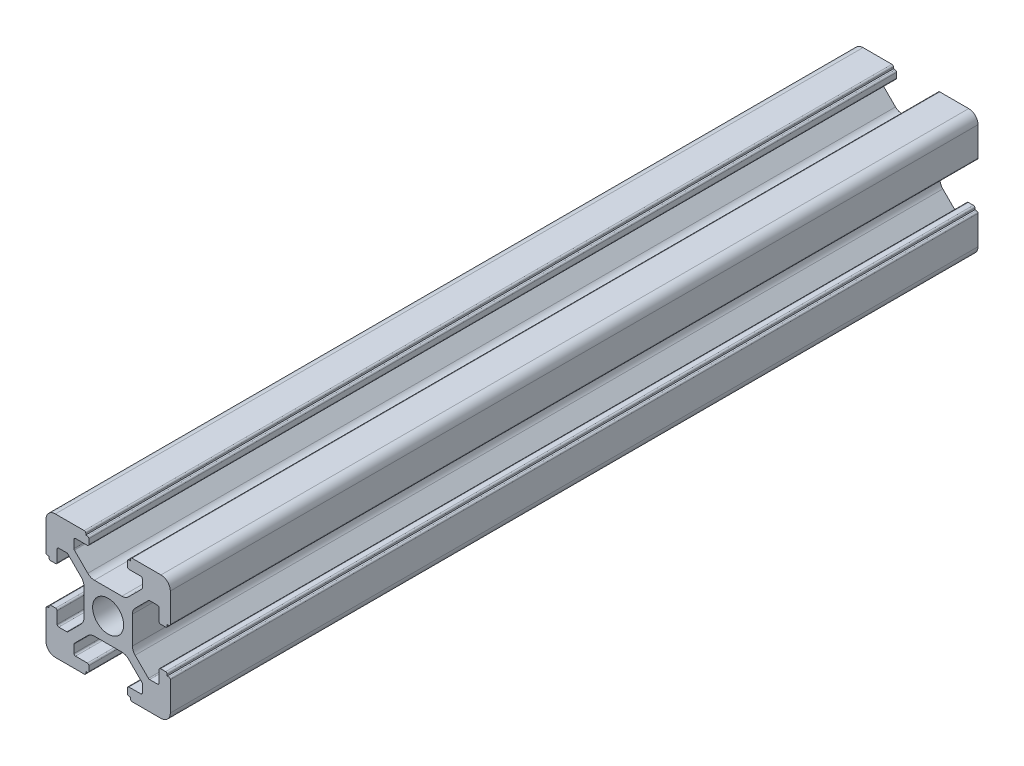
SolidWorks part; units mm, degrees
material "1060 Alloy"
ref_plane "前视基准面" through (0, 0, 0) normal (0, 0, 1) x (1, 0, 0)
ref_plane "上视基准面" through (0, 0, 0) normal (0, 1, 0) x (1, 0, 0)
ref_plane "右视基准面" through (0, 0, 0) normal (1, 0, 0) x (0, 0, -1)
sketch "草图1" plane through (0, 0, 0) normal (0, 0, 1) x (1, 0, 0)
  line L0 (0, 0) -> (0, 5.5) construction
  line L1 (-8.5023, -10.0023) -> (-3.85, -10.0023)
  line L2 (-10.0023, -8.5023) -> (-10.0023, -3.85)
  line L3 (-8.5023, 10.0023) -> (-3.85, 10.0023)
  line L4 (10.0023, -8.5023) -> (10.0023, -3.85)
  line L5 (-10.0023, -10.0023) -> (10.0023, 10.0023) construction
  line L6 (-10.0023, 10.0023) -> (10.0023, -10.0023) construction
  line L7 (-2.218, -3.9) -> (2.218, -3.9)
  line L8 (-3.9, -2.218) -> (-3.9, 2.218)
  line L9 (-2.218, 3.9) -> (2.218, 3.9)
  line L10 (3.9, -2.218) -> (3.9, 2.218)
  line L11 (-3.9, -3.9) -> (3.9, 3.9) construction
  line L12 (-3.9, 3.9) -> (3.9, -3.9) construction
  line L13 (-5.25, -8.2) -> (-3.35, -8.2)
  line L14 (-8.2, -5.25) -> (-8.2, -3.35)
  line L15 (-5.25, 8.2) -> (-3.35, 8.2)
  line L16 (8.2, -5.25) -> (8.2, -3.35)
  line L17 (-8.2, -8.2) -> (8.2, 8.2) construction
  line L18 (-8.2, 8.2) -> (8.2, -8.2) construction
  line L19 (-7.95, 5.5) -> (-6.6642, 5.5)
  line L20 (0, 0) -> (5.5, 0) construction
  line L23 (-5.5, 7.95) -> (-5.5, 6.6642)
  line L26 (0, 0) -> (-0.5303, 0.5303)
  line L27 (3.2787, 4.3393) -> (5.4268, 6.4874)
  line L28 (0, 0) -> (0.5303, -0.5303)
  line L29 (5.5, 6.6642) -> (5.5, 7.95)
  line L30 (4.3393, 3.2787) -> (6.4874, 5.4268)
  line L31 (6.6642, 5.5) -> (7.95, 5.5)
  line L32 (4.3393, -3.2787) -> (6.4874, -5.4268)
  line L33 (3.2787, -4.3393) -> (5.4268, -6.4874)
  line L34 (-3.2787, -4.3393) -> (-5.4268, -6.4874)
  line L35 (-4.3393, -3.2787) -> (-6.4874, -5.4268)
  line L36 (-4.3393, 3.2787) -> (-6.4874, 5.4268)
  line L37 (-3.2787, 4.3393) -> (-5.4268, 6.4874)
  line L38 (3.1, -8.45) -> (3.1, -9.2523)
  line L39 (8.45, 3.1) -> (9.2523, 3.1)
  line L40 (-5.5, -6.6642) -> (-5.5, -7.95)
  line L41 (-6.6642, -5.5) -> (-7.95, -5.5)
  line L42 (5.5, -6.6642) -> (5.5, -7.95)
  line L43 (6.6642, -5.5) -> (7.95, -5.5)
  line L44 (9.2523, -3.1) -> (8.45, -3.1)
  line L46 (10.0023, 3.85) -> (10.0023, 8.5023)
  line L47 (8.2, 3.35) -> (8.2, 5.25)
  line L48 (-3.1, -9.2523) -> (-3.1, -8.45)
  line L49 (-8.45, -3.1) -> (-9.2523, -3.1)
  line L50 (-9.2523, 3.1) -> (-8.45, 3.1)
  line L51 (-3.1, 8.45) -> (-3.1, 9.2523)
  line L52 (3.1, 9.2523) -> (3.1, 8.45)
  line L53 (3.85, 10.0023) -> (8.5023, 10.0023)
  line L54 (3.35, 8.2) -> (5.25, 8.2)
  line L55 (-10.0023, 3.85) -> (-10.0023, 8.5023)
  line L56 (-8.2, 3.35) -> (-8.2, 5.25)
  line L57 (3.35, -8.2) -> (5.25, -8.2)
  line L58 (3.85, -10.0023) -> (8.5023, -10.0023)
  line L59 (9.7523, -3.6) -> (9.5023, -3.6)
  line L61 (9.7523, 3.6) -> (9.5023, 3.6)
  line L62 (9.5023, -3.6) -> (9.5023, -3.35)
  line L63 (3.6, -9.7523) -> (3.6, -9.5023)
  line L64 (3.35, -9.5023) -> (3.6, -9.5023)
  line L65 (9.5023, 3.35) -> (9.5023, 3.6)
  line L66 (-3.6, -9.5023) -> (-3.35, -9.5023)
  line L67 (-3.6, -9.7523) -> (-3.6, -9.5023)
  line L68 (-9.7523, -3.6) -> (-9.5023, -3.6)
  line L69 (-9.5023, -3.35) -> (-9.5023, -3.6)
  line L70 (-9.5023, 3.6) -> (-9.5023, 3.35)
  line L71 (-9.7523, 3.6) -> (-9.5023, 3.6)
  line L72 (-3.6, 9.7523) -> (-3.6, 9.5023)
  line L73 (-3.35, 9.5023) -> (-3.6, 9.5023)
  line L74 (3.6, 9.5023) -> (3.35, 9.5023)
  line L75 (3.6, 9.7523) -> (3.6, 9.5023)
  circle A0 centre (0, 0) radius 2.5
  arc A1 (10.0023, 8.5023) -> (8.5023, 10.0023) centre (8.5023, 8.5023) ccw
  arc A2 (8.5023, -10.0023) -> (10.0023, -8.5023) centre (8.5023, -8.5023) ccw
  arc A3 (-10.0023, -8.5023) -> (-8.5023, -10.0023) centre (-8.5023, -8.5023) ccw
  arc A4 (-10.0023, 8.5023) -> (-8.5023, 10.0023) centre (-8.5023, 8.5023) cw
  arc A5 (-9.5023, -3.35) -> (-9.2523, -3.1) centre (-9.2523, -3.35) cw
  arc A6 (-9.7523, -3.6) -> (-10.0023, -3.85) centre (-9.7523, -3.85) ccw
  arc A7 (-8.45, -3.1) -> (-8.2, -3.35) centre (-8.45, -3.35) cw
  arc A8 (-7.95, -5.5) -> (-8.2, -5.25) centre (-7.95, -5.25) cw
  arc A9 (-6.4874, -5.4268) -> (-6.6642, -5.5) centre (-6.6642, -5.25) cw
  arc A10 (-5.4268, -6.4874) -> (-5.5, -6.6642) centre (-5.25, -6.6642) ccw
  arc A11 (-5.5, -7.95) -> (-5.25, -8.2) centre (-5.25, -7.95) ccw
  arc A12 (-3.6, -9.7523) -> (-3.85, -10.0023) centre (-3.85, -9.7523) cw
  arc A13 (-3.35, -9.5023) -> (-3.1, -9.2523) centre (-3.35, -9.2523) ccw
  arc A14 (-3.1, -8.45) -> (-3.35, -8.2) centre (-3.35, -8.45) ccw
  arc A15 (3.1, -8.45) -> (3.35, -8.2) centre (3.35, -8.45) cw
  arc A16 (5.5, -7.95) -> (5.25, -8.2) centre (5.25, -7.95) cw
  arc A17 (5.4268, -6.4874) -> (5.5, -6.6642) centre (5.25, -6.6642) cw
  arc A18 (6.4874, -5.4268) -> (6.6642, -5.5) centre (6.6642, -5.25) ccw
  arc A19 (7.95, -5.5) -> (8.2, -5.25) centre (7.95, -5.25) ccw
  arc A20 (8.45, -3.1) -> (8.2, -3.35) centre (8.45, -3.35) ccw
  arc A21 (9.5023, -3.35) -> (9.2523, -3.1) centre (9.2523, -3.35) ccw
  arc A22 (9.7523, -3.6) -> (10.0023, -3.85) centre (9.7523, -3.85) cw
  arc A23 (3.35, -9.5023) -> (3.1, -9.2523) centre (3.35, -9.2523) cw
  arc A24 (3.6, -9.7523) -> (3.85, -10.0023) centre (3.85, -9.7523) ccw
  arc A25 (7.95, 5.5) -> (8.2, 5.25) centre (7.95, 5.25) cw
  arc A26 (8.2, 3.35) -> (8.45, 3.1) centre (8.45, 3.35) ccw
  arc A27 (9.5023, 3.35) -> (9.2523, 3.1) centre (9.2523, 3.35) cw
  arc A28 (9.7523, 3.6) -> (10.0023, 3.85) centre (9.7523, 3.85) ccw
  arc A29 (6.6642, 5.5) -> (6.4874, 5.4268) centre (6.6642, 5.25) ccw
  arc A30 (5.4268, 6.4874) -> (5.5, 6.6642) centre (5.25, 6.6642) ccw
  arc A31 (5.5, 7.95) -> (5.25, 8.2) centre (5.25, 7.95) ccw
  arc A32 (3.1, 8.45) -> (3.35, 8.2) centre (3.35, 8.45) ccw
  arc A33 (3.6, 9.7523) -> (3.85, 10.0023) centre (3.85, 9.7523) cw
  arc A34 (3.35, 9.5023) -> (3.1, 9.2523) centre (3.35, 9.2523) ccw
  arc A35 (-9.7523, 3.6) -> (-10.0023, 3.85) centre (-9.7523, 3.85) cw
  arc A36 (-9.5023, 3.35) -> (-9.2523, 3.1) centre (-9.2523, 3.35) ccw
  arc A37 (-8.45, 3.1) -> (-8.2, 3.35) centre (-8.45, 3.35) ccw
  arc A38 (-8.2, 5.25) -> (-7.95, 5.5) centre (-7.95, 5.25) cw
  arc A39 (-6.4874, 5.4268) -> (-6.6642, 5.5) centre (-6.6642, 5.25) ccw
  arc A40 (-5.4268, 6.4874) -> (-5.5, 6.6642) centre (-5.25, 6.6642) cw
  arc A41 (-5.5, 7.95) -> (-5.25, 8.2) centre (-5.25, 7.95) cw
  arc A42 (-3.1, 8.45) -> (-3.35, 8.2) centre (-3.35, 8.45) cw
  arc A43 (-3.1, 9.2523) -> (-3.35, 9.5023) centre (-3.35, 9.2523) ccw
  arc A44 (-3.6, 9.7523) -> (-3.85, 10.0023) centre (-3.85, 9.7523) ccw
  arc A45 (-4.3393, 3.2787) -> (-3.9, 2.218) centre (-5.4, 2.218) cw
  arc A46 (-3.2787, 4.3393) -> (-2.218, 3.9) centre (-2.218, 5.4) ccw
  arc A47 (3.2787, 4.3393) -> (2.218, 3.9) centre (2.218, 5.4) cw
  arc A48 (4.3393, 3.2787) -> (3.9, 2.218) centre (5.4, 2.218) ccw
  arc A49 (4.3393, -3.2787) -> (3.9, -2.218) centre (5.4, -2.218) cw
  arc A50 (3.2787, -4.3393) -> (2.218, -3.9) centre (2.218, -5.4) ccw
  arc A51 (-4.3393, -3.2787) -> (-3.9, -2.218) centre (-5.4, -2.218) ccw
  arc A52 (-2.218, -3.9) -> (-3.2787, -4.3393) centre (-2.218, -5.4) ccw
  point P0 (0, 0)
  point P7 (10.0023, 0)
  point P62 (0, 0)
  point P76 (0, 0)
  point P92 (-8.2, -5.5)
  point P99 (0, 0)
  point P106 (-5.5, -8.2)
  point P117 (5.5, -8.2)
  point P124 (8.2, -5.5)
  point P137 (8.2, 5.5)
  point P140 (8.2, 3.1)
  point P147 (6.5607, 5.5)
  point P152 (5.5, 8.2)
  point P167 (-8.2, 5.5)
  point P174 (-5.5, 8.2)
  dimension "D1" = 1.5
  dimension "D5" = 0.25
  dimension "D6" = 1.5
  dimension "D2" = 4
  dimension "D3" = 4
  dimension "D4" = 4
extrude "凸台-拉伸1" add sketch "草图1" along normal blind 130 contours A52 L7 A50 L33 A17 L42 A16 L57 A15 L38 A23 L64 L63 A24 L58 A2 L4 A22 L59 L62 A21 L44 A20 L16 A19 L43 A18 L32 A49 L10 A48 L30 A29 L31 A25 L47 A26 L39 A27 L65 L61 A28 L46 A1 L53 A33 L75 L74 A34 L52 A32
ref_plane "Plane1" through (0, 0, 65) normal (0, 0, 1) x (1, 0, 0)
